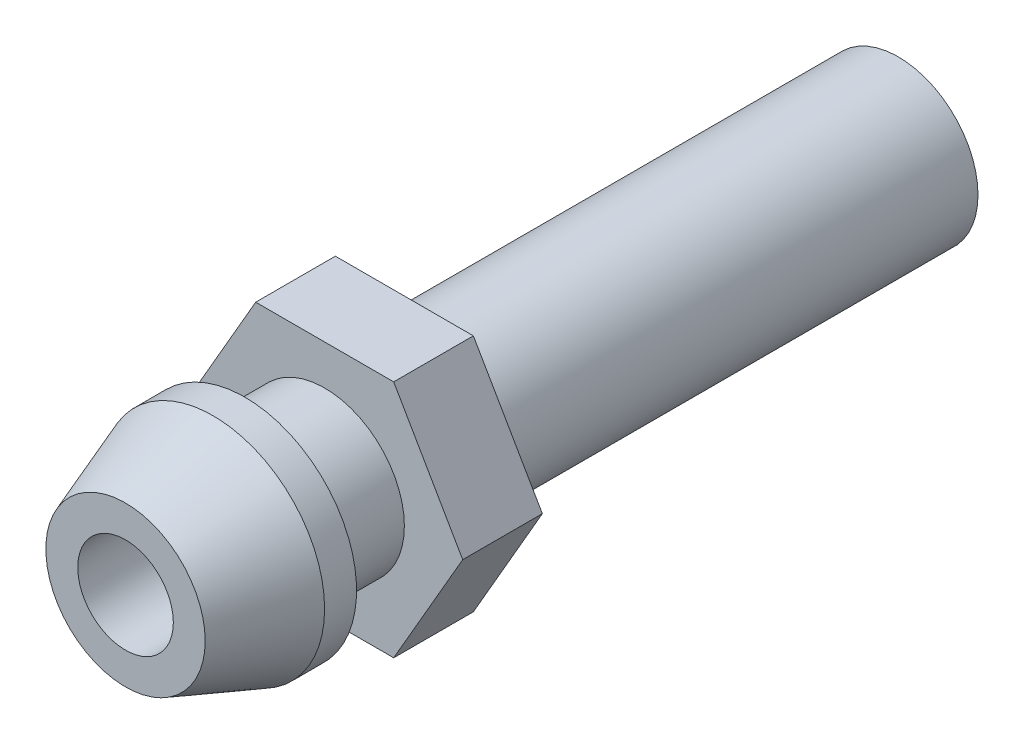
SolidWorks part; units mm, degrees
material "Plain Carbon Steel"
ref_plane "Front Plane" through (0, 0, 0) normal (0, 0, 1) x (1, 0, 0)
ref_plane "Top Plane" through (0, 0, 0) normal (0, 1, 0) x (1, 0, 0)
ref_plane "Right Plane" through (0, 0, 0) normal (1, 0, 0) x (0, 0, -1)
sketch "Sketch1" plane through (0, 0, 0) normal (0, 0, 1) x (1, 0, 0)
  circle A0 centre (0, 0) radius 1.27
  dimension "D1" = 2.54
extrude "Boss-Extrude1" add sketch "Sketch1" along normal blind 6.35
sketch "Sketch2" plane through (0, 0, 6.35) normal (0, 0, 1) x (1, 0, 0)
  circle A0 centre (0, 0) radius 1.27
  dimension "D1" = 2.54
extrude "Boss-Extrude2" add sketch "Sketch2" along normal blind 0.254
sketch "Sketch3" plane through (0, 0, 6.604) normal (0, 0, 1) x (1, 0, 0)
  circle A0 centre (0, 0) radius 1.27
  dimension "D1" = 2.54
extrude "Boss-Extrude3" add sketch "Sketch3" along normal blind 1.27
sketch "Sketch4" plane through (0, 0, 7.874) normal (0, 0, 1) x (1, 0, 0)
  line L1 (2.1997, 0) -> (1.0999, 1.905)
  line L2 (1.0999, 1.905) -> (-1.0999, 1.905)
  line L3 (-1.0999, 1.905) -> (-2.1997, 0)
  line L4 (-2.1997, 0) -> (-1.0999, -1.905)
  line L5 (-1.0999, -1.905) -> (1.0999, -1.905)
  line L6 (1.0999, -1.905) -> (2.1997, 0)
  circle A0 centre (0, 0) radius 1.905 construction
  dimension "D1" = 3.81
extrude "Boss-Extrude4" add sketch "Sketch4" along normal blind 1.27
sketch "Sketch5" plane through (0, 0, 9.144) normal (0, 0, 1) x (1, 0, 0)
  circle A0 centre (0, 0) radius 1.27
  dimension "D1" = 2.54
extrude "Boss-Extrude5" add sketch "Sketch5" along normal blind 1.27
sketch "Sketch6" plane through (0, 0, 10.414) normal (0, 0, 1) x (1, 0, 0)
  circle A0 centre (0, 0) radius 1.27
  dimension "D1" = 2.54
extrude "Boss-Extrude6" add sketch "Sketch6" along normal blind 1.905 separate body
draft "Draft3" type of draft neutral plane draft angle 20 faces to draft 1 face at (1.27, 0, 12.319) neutral plane through (0, 0, 12.319) neutral plane normal (0, 0, 1) parameters "D1"=20
sketch "Sketch7" plane through (0, 0, 12.319) normal (0, 0, 1) x (1, 0, 0)
  circle A0 centre (0, 0) radius 0.762
  dimension "D1" = 1.524
extrude "Cut-Extrude1" cut sketch "Sketch7" against normal through all
sketch "Sketch8" plane through (0, 0, 10.414) normal (0, 0, -1) x (-1, 0, 0)
  circle A0 centre (0, 0) radius 1.778
  circle A1 centre (0, 0) radius 1.9634
extrude "Cut-Extrude2" cut sketch "Sketch8" against normal blind 2.54
